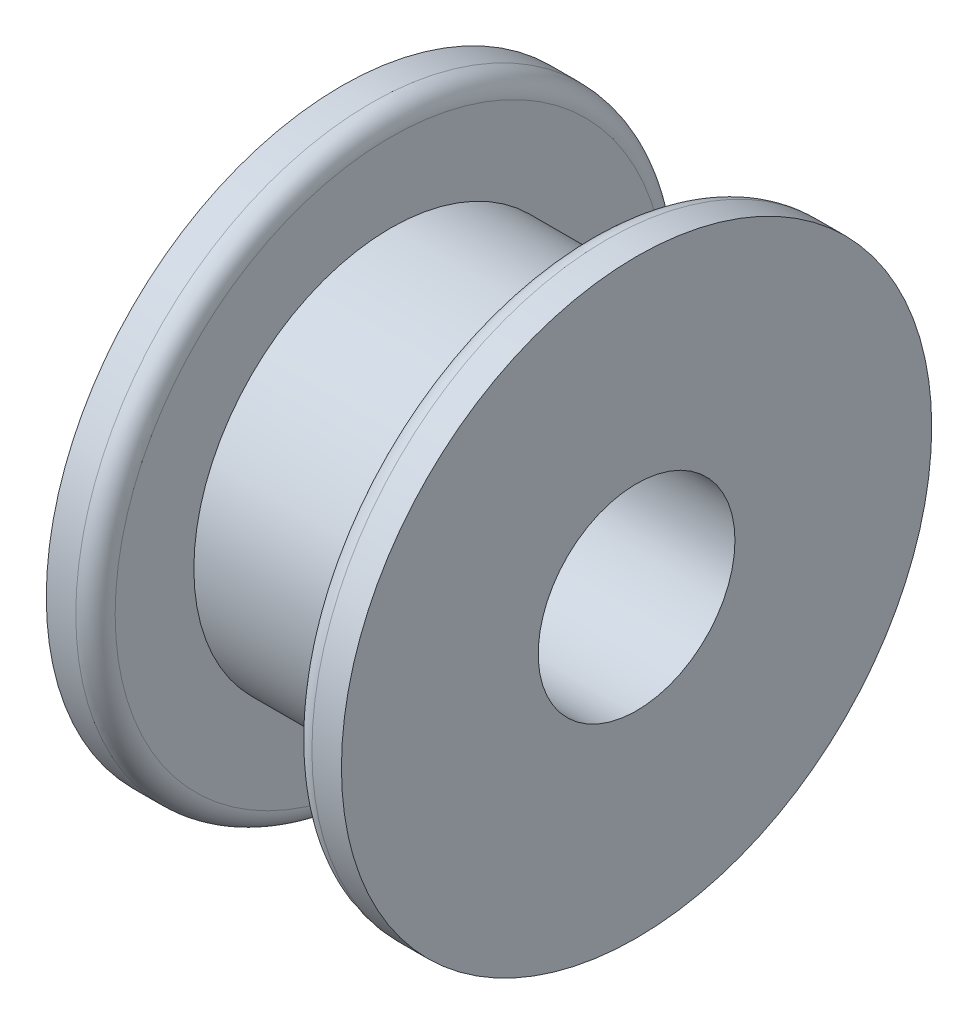
SolidWorks part; units mm, degrees
ref_plane "Front Plane" through (0, 0, 0) normal (0, 0, 1) x (1, 0, 0)
ref_plane "Top Plane" through (0, 0, 0) normal (0, 1, 0) x (1, 0, 0)
ref_plane "Right Plane" through (0, 0, 0) normal (1, 0, 0) x (0, 0, -1)
sketch "Sketch1" plane through (0, 0, 0) normal (1, 0, 0) x (0, 0, -1)
  circle A0 centre (0, 0) radius 12.7
extrude "Boss-Extrude1" add sketch "Sketch1" along normal blind 6.35
sketch "Sketch2" plane through (6.35, 0, 0) normal (1, 0, 0) x (0, 0, -1)
  circle A0 centre (0, 0) radius 19.05
extrude "Boss-Extrude2" add sketch "Sketch2" along normal blind 3.175
fillet "Fillet1" radius 1.27 1 edges at (6.35, 0, -19.05)
mirror "Mirror1" about plane through (0, 0, 0) normal (1, 0, 0) of "Fillet1", "Boss-Extrude1", "Boss-Extrude2"
sketch "Sketch3" plane through (9.525, 0, 0) normal (1, 0, 0) x (0, 0, -1)
  circle A0 centre (0, 0) radius 6.35
extrude "Cut-Extrude1" cut sketch "Sketch3" against normal up to next
